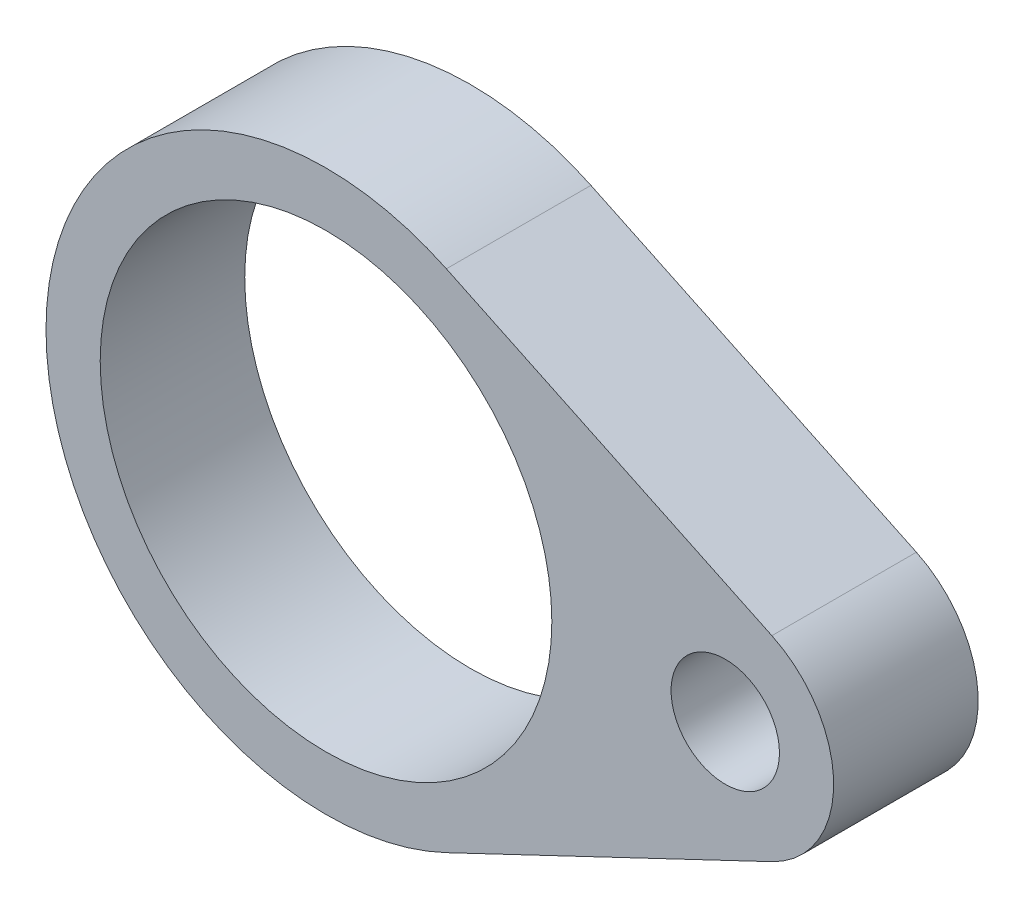
SolidWorks part; units mm, degrees
material "普通碳钢"
ref_plane "前视基准面" through (0, 0, 0) normal (0, 0, 1) x (1, 0, 0)
ref_plane "上视基准面" through (0, 0, 0) normal (0, 1, 0) x (1, 0, 0)
ref_plane "右视基准面" through (0, 0, 0) normal (1, 0, 0) x (0, 0, -1)
sketch "草图1" plane through (0, 0, 0) normal (0, 0, 1) x (1, 0, 0)
  line L0 (0, 0) -> (22.1, 0) construction
  line L1 (6.6629, 13.9948) -> (24.6792, 5.4174)
  line L2 (24.6792, -5.4174) -> (6.6629, -13.9948)
  circle A0 centre (0, 0) radius 12.5
  arc A1 (6.6629, 13.9948) -> (6.6629, -13.9948) centre (0, 0) ccw
  circle A2 centre (22.1, 0) radius 3
  arc A3 (24.6792, -5.4174) -> (24.6792, 5.4174) centre (22.1, 0) ccw
  dimension "D1" = 22.1
  dimension "D2" = 25
  dimension "D3" = 31
  dimension "D4" = 12
  dimension "D5" = 6
extrude "凸台-拉伸1" add sketch "草图1" along normal blind 8
